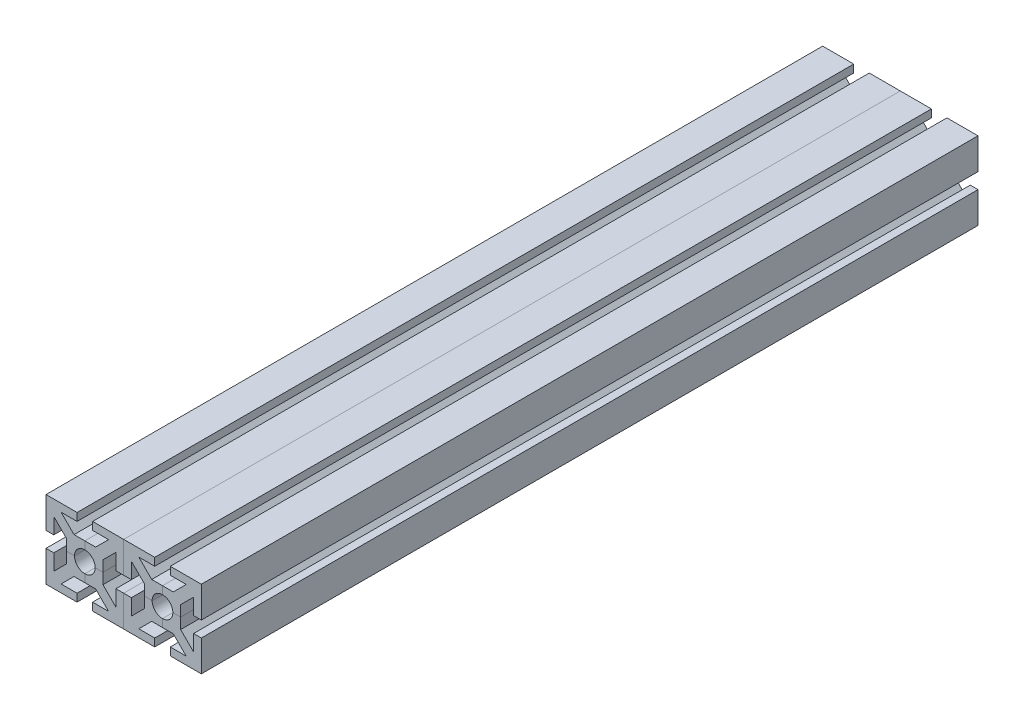
SolidWorks part; units mm, degrees
ref_plane "Alzado" through (0, 0, 0) normal (0, 0, 1) x (1, 0, 0)
ref_plane "Planta" through (0, 0, 0) normal (0, 1, 0) x (1, 0, 0)
ref_plane "Vista lateral" through (0, 0, 0) normal (1, 0, 0) x (0, 0, -1)
sketch "Croquis1" plane through (0, 0, 0) normal (0, 0, 1) x (1, 0, 0)
  line L0 (0, 0) -> (50000, 0) construction
  line L1 (-15, 15) -> (15, 15) construction
  line L2 (-15, 15) -> (-15, -15) construction
  line L3 (-15, -15) -> (15, -15) construction
  line L4 (15, 15) -> (15, -15) construction
  line L5 (-15, 15) -> (15, -15) construction
  line L6 (-15, -15) -> (15, 15) construction
  line L7 (0, 0) -> (0, -50000) construction
  line L8 (0, 4) -> (0, 7)
  line L9 (0, 7) -> (4.1716, 7)
  line L10 (4.1716, 7) -> (9.1716, 12)
  line L11 (9.1716, 12) -> (3, 12)
  line L12 (3, 12) -> (3, 15)
  line L13 (3, 15) -> (15, 15)
  line L20 (2.8284, 2.8284) -> (15, 15)
  arc A0 (2.8284, 2.8284) -> (0, 4) centre (0, 0) ccw
  point P0 (0, 0)
  dimension "D3" = 4
  dimension "D1" = 30
  dimension "D2" = 6
  dimension "D4" = 8
  dimension "D5" = 3
  dimension "D6" = 2
extrude "Saliente-Extruir1" add sketch "Croquis1" along normal mid plane 300
mirror "Simetría1" about plane through (2.8284, 2.8284, 150) normal (-0.7071, 0.7071, 0) of "Saliente-Extruir1"
pattern_circular "MatrizC4" count 4 over 360 about axis through (0, 0, 0) along (0, 0, 1) of bodies 102
mirror "Simetría2" about plane through (15, 3, 150) normal (1, 0, 0) of bodies 104 105 103 102
